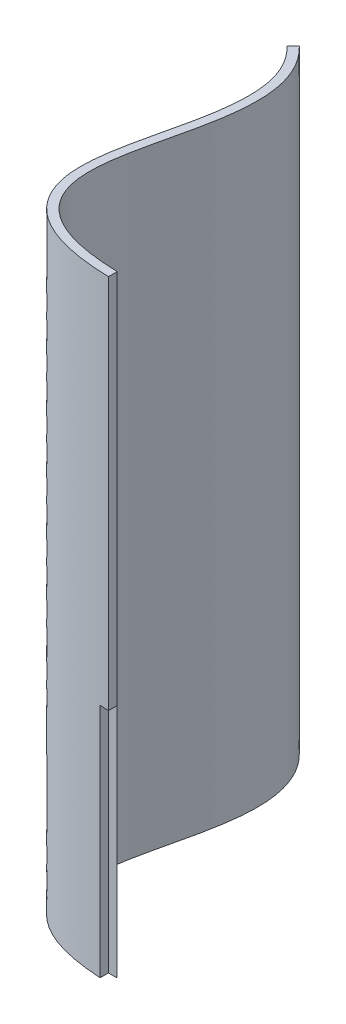
SolidWorks part; units mm, degrees
ref_plane "Alzado" through (0, 0, 0) normal (0, 0, 1) x (1, 0, 0)
ref_plane "Planta" through (0, 0, 0) normal (0, 1, 0) x (1, 0, 0)
ref_plane "Vista lateral" through (0, 0, 0) normal (1, 0, 0) x (0, 0, -1)
sketch "Croquis1" plane through (0, 0, 0) normal (0, 1, 0) x (1, 0, 0)
  line L1 (-47.2892, -73.7815) -> (-17.2892, -73.7815)
  line L2 (-47.2892, -73.7815) -> (-47.2892, 6.2185)
  line L3 (-47.2892, 6.2185) -> (-17.2892, 6.2185)
  line L4 (-17.2892, -73.7815) -> (-17.2892, 6.2185)
extrude "Saliente-Extruir1" add sketch "Croquis1" along normal blind 140
sketch "Croquis2" plane through (0, 140, 0) normal (0, 1, 0) x (1, 0, 0)
  line L0 (-17.2892, -73.7815) -> (-17.2892, -71.7806)
  line L1 (-17.2892, -73.7815) -> (-17.2892, 6.2185) construction
  line L2 (-42.555, -7.6597) -> (-41.168, -6.2188)
  line L3 (-17.2892, -71.7806) -> (-17.2892, 6.2185)
  line L4 (-17.2892, 6.2185) -> (-47.2892, 6.2185)
  line L5 (-47.2892, 6.2185) -> (-47.2892, -73.7815)
  line L6 (-47.2892, 6.2185) -> (-47.2892, -73.7815) construction
  line L7 (-47.2892, -73.7815) -> (-17.2892, -73.7815)
  spline S0 degree 3 poles (-17.2892, -73.7815) (-18.0288, -73.7602) (-19.5367, -73.6943) (-21.6192, -73.5342) (-23.6003, -73.3109) (-26.0853, -72.9297) (-28.9236, -72.2957) (-31.9256, -71.2785) (-34.5566, -69.9885) (-37.556, -67.9076) (-40.3409, -64.6107) (-42.0411, -59.9883) (-42.4699, -55.1344) (-42.0642, -50.1182) (-40.8214, -43.2476) (-39.0462, -36.1698) (-37.6704, -29.2152) (-37.0544, -24.1735) (-37.0519, -19.4298) (-37.6927, -15.813) (-38.6615, -13.1337) (-39.6388, -11.2231) (-40.6936, -9.6989) (-41.6953, -8.5241) (-42.265, -7.9389) (-42.555, -7.6597) knots 0 0 0 0 0.015253 0.030506 0.045759 0.061012 0.091518 0.122023 0.152529 0.183035 0.244047 0.305059 0.36607 0.427082 0.488094 0.610117 0.671129 0.732141 0.793152 0.854164 0.88467 0.915176 0.945682 0.960935 0.976187 0.976187 0.976187 0.976187
  spline S1 degree 1 poles (-17.2316, -71.7823) (-41.168, -6.2188) knots 0 0 1 1 construction
  spline S2 degree 3 poles (-17.2316, -71.7823) (-17.9508, -71.7616) (-19.4198, -71.6974) (-21.4318, -71.5426) (-23.3393, -71.3274) (-25.7134, -70.9631) (-28.395, -70.3629) (-31.172, -69.42) (-33.5514, -68.2507) (-36.1874, -66.4172) (-38.5723, -63.5887) (-40.0584, -59.58) (-40.4614, -55.1591) (-40.0812, -50.3995) (-38.8735, -43.7075) (-37.1011, -36.6376) (-35.6963, -29.5467) (-35.055, -24.3169) (-35.0472, -19.2812) (-35.7425, -15.3232) (-36.821, -12.3373) (-37.9184, -10.1917) (-39.0996, -8.485) (-40.2181, -7.1736) (-40.8471, -6.5278) (-41.168, -6.2188) knots 0 0 0 0 0.015253 0.030506 0.045759 0.061012 0.091518 0.122023 0.152529 0.183035 0.244047 0.305059 0.36607 0.427082 0.488094 0.610117 0.671129 0.732141 0.793152 0.854164 0.88467 0.915176 0.945682 0.960935 0.976187 0.976187 0.976187 0.976187 only from (-17.2892, -71.7806) to (-41.168, -6.2188)
  line M1 (-47.2892, 6.2185) -> (-47.2892, -73.7815)
  line M2 (-47.2892, -73.7815) -> (-17.2892, -73.7815)
  line M3 (-17.2892, -73.7815) -> (-17.2892, 6.2185)
  line M4 (-17.2892, 6.2185) -> (-47.2892, 6.2185)
extrude "Cortar-Extruir1" cut sketch "Croquis2" against normal through all contours S2 S0 L2 M3 M4 M1 M2
sketch "Croquis3" plane through (-17.2892, 0, 0) normal (1, 0, 0) x (0, 0, -1)
  line L0 (-73.7815, 0) -> (-73.7815, 54)
  line L1 (-73.7815, 140) -> (-73.7815, 0) construction
  line L2 (-73.7815, 54) -> (-71.7806, 54)
  line L3 (-71.7806, 0) -> (-71.7806, 140) construction
  line L4 (-71.7806, 54) -> (-71.7806, 0)
  line L5 (-71.7806, 0) -> (-73.7815, 0)
extrude "Cortar-Extruir2" cut sketch "Croquis3" against normal blind 2
